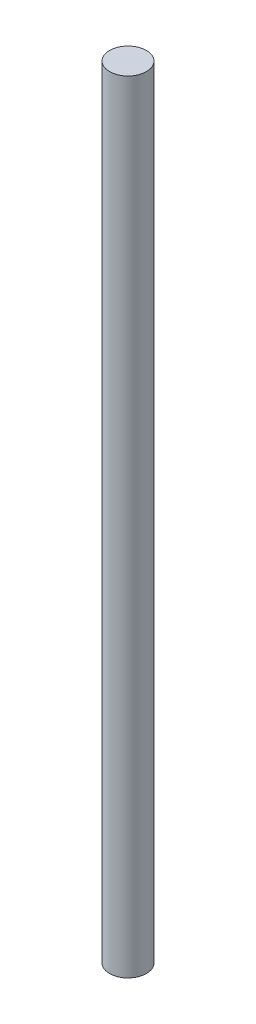
SolidWorks part; units mm, degrees
ref_plane "Front Plane" through (0, 0, 0) normal (0, 0, 1) x (1, 0, 0)
ref_plane "Top Plane" through (0, 0, 0) normal (0, 1, 0) x (1, 0, 0)
ref_plane "Right Plane" through (0, 0, 0) normal (1, 0, 0) x (0, 0, -1)
sketch "Sketch1" plane through (0, 0, 0) normal (0, 1, 0) x (1, 0, 0)
  circle A0 centre (0, 0) radius 4
extrude "Boss-Extrude1" add sketch "Sketch1" along normal blind 169.9624
